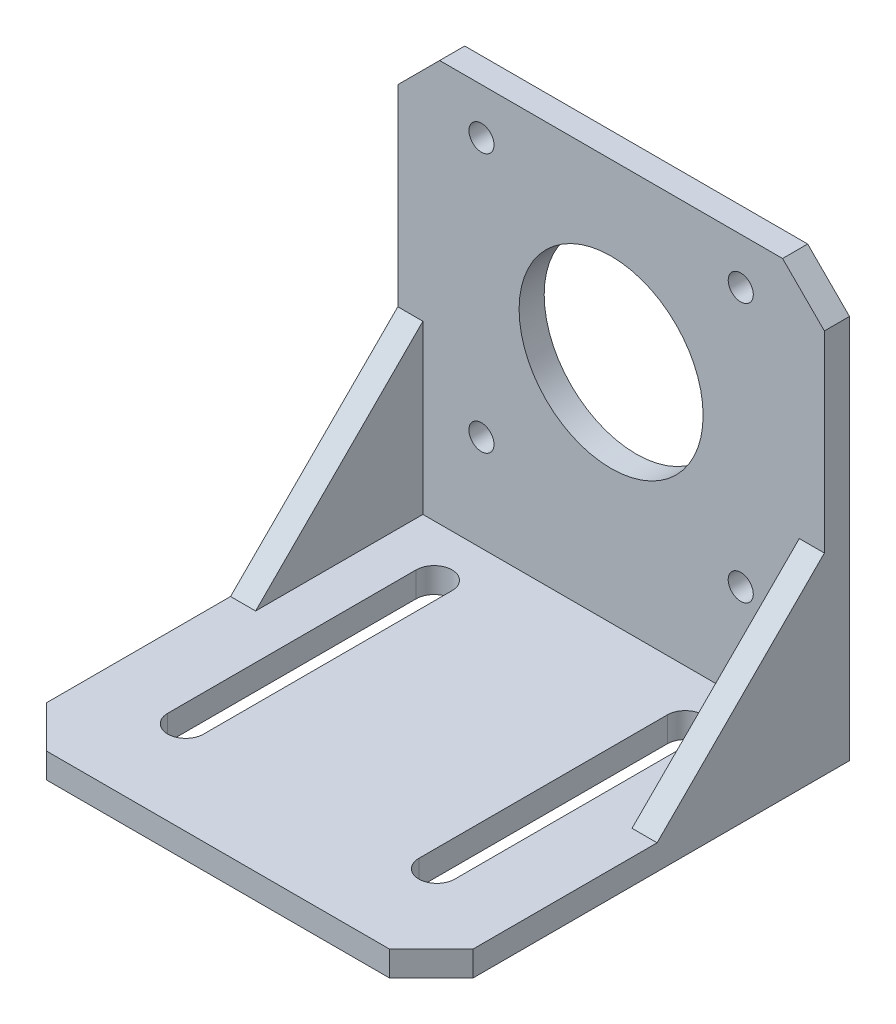
SolidWorks part; units mm, degrees
ref_plane "Front Plane" through (0, 0, 0) normal (0, 0, 1) x (1, 0, 0)
ref_plane "Top Plane" through (0, 0, 0) normal (0, 1, 0) x (1, 0, 0)
ref_plane "Right Plane" through (0, 0, 0) normal (1, 0, 0) x (0, 0, -1)
sketch "Sketch1" plane through (0, 0, 0) normal (0, 1, 0) x (1, 0, 0)
  line L0 (-15.015, 15.85) -> (-15.015, -13.85) construction
  line L1 (25.5, -25) -> (-25.5, -25)
  line L2 (25.5, -25) -> (25.5, 25)
  line L3 (25.5, 25) -> (-25.5, 25)
  line L4 (-25.5, -25) -> (-25.5, 25)
  line L5 (25.5, -25) -> (-25.5, 25) construction
  line L6 (25.5, 25) -> (-25.5, -25) construction
  line L7 (-12.865, 15.85) -> (-12.865, -13.85)
  line L8 (-17.165, 15.85) -> (-17.165, -13.85)
  line L9 (0, 25) -> (0, -25) construction
  line L10 (15.015, 15.85) -> (15.015, -13.85) construction
  line L11 (12.865, 15.85) -> (12.865, -13.85)
  line L12 (17.165, 15.85) -> (17.165, -13.85)
  arc A0 (-12.865, 15.85) -> (-17.165, 15.85) centre (-15.015, 15.85) ccw
  arc A1 (-17.165, -13.85) -> (-12.865, -13.85) centre (-15.015, -13.85) ccw
  arc A2 (12.865, 15.85) -> (17.165, 15.85) centre (15.015, 15.85) cw
  arc A3 (17.165, -13.85) -> (12.865, -13.85) centre (15.015, -13.85) cw
  point P0 (0, 0)
  point P8 (-15.015, 1)
  point P13 (-15.015, -16)
  point P14 (-15.015, 18)
  point P15 (0, 0)
  point P20 (15.015, 1)
  dimension "D1" = 51
  dimension "D2" = 50
  dimension "D3" = 4.3
  dimension "D4" = 34
  dimension "D5" = 9
  dimension "D6" = 25.73
extrude "Boss-Extrude1" add sketch "Sketch1" along normal blind 3
sketch "Sketch2" plane through (0, 0, 0) normal (0, -1, 0) x (1, 0, 0)
  line L0 (25.5, 25) -> (25.5, -25) construction
  line L1 (-25.5, -25) -> (25.5, -25)
  line L2 (-25.5, -25) -> (-25.5, -22)
  line L3 (-25.5, -22) -> (25.5, -22)
  line L4 (25.5, -25) -> (25.5, -22)
  dimension "D1" = 3
extrude "Boss-Extrude2" add sketch "Sketch2" against normal blind 51
sketch "Sketch3" plane through (0, 0, -22) normal (0, 0, 1) x (1, 0, 0)
  line L0 (0, 0) -> (0, 51) construction
  line L1 (25.5, 51) -> (-25.5, 51) construction
  line L2 (0, 30) -> (-25.5, 30) construction
  line L3 (-25.5, 51) -> (-25.5, 3) construction
  circle A0 centre (0, 30) radius 11
  circle A1 centre (-15.5, 45.5) radius 1.5
  circle A2 centre (15.5, 45.5) radius 1.5
  circle A3 centre (-15.5, 14.5) radius 1.5
  circle A4 centre (15.5, 14.5) radius 1.5
  dimension "D1" = 22
  dimension "D3" = 3
  dimension "D2" = 21
  dimension "D4" = 31
  dimension "D5" = 31
extrude "Cut-Extrude1" cut sketch "Sketch3" against normal through all
sketch "Sketch5" plane through (-25.5, 0, 0) normal (-1, 0, 0) x (0, 0, 1)
  line L0 (-22, 23) -> (-2, 3)
  line L1 (-22, 51) -> (-22, 3) construction
  line L2 (-22, 3) -> (25, 3) construction
  line L3 (-2, 3) -> (-22, 3)
  line L4 (-22, 3) -> (-22, 23)
  dimension "D1" = 20
extrude "Boss-Extrude3" add sketch "Sketch5" against normal blind 3
mirror "Mirror1" about plane through (0, 0, 0) normal (1, 0, 0) of "Boss-Extrude3"
chamfer "Chamfer1" distance 5 angle 45 4 edges at (-25.5, 1.5, 25) (25.5, 1.5, 25) (-25.5, 51, -23.5) (25.5, 51, -23.5)
